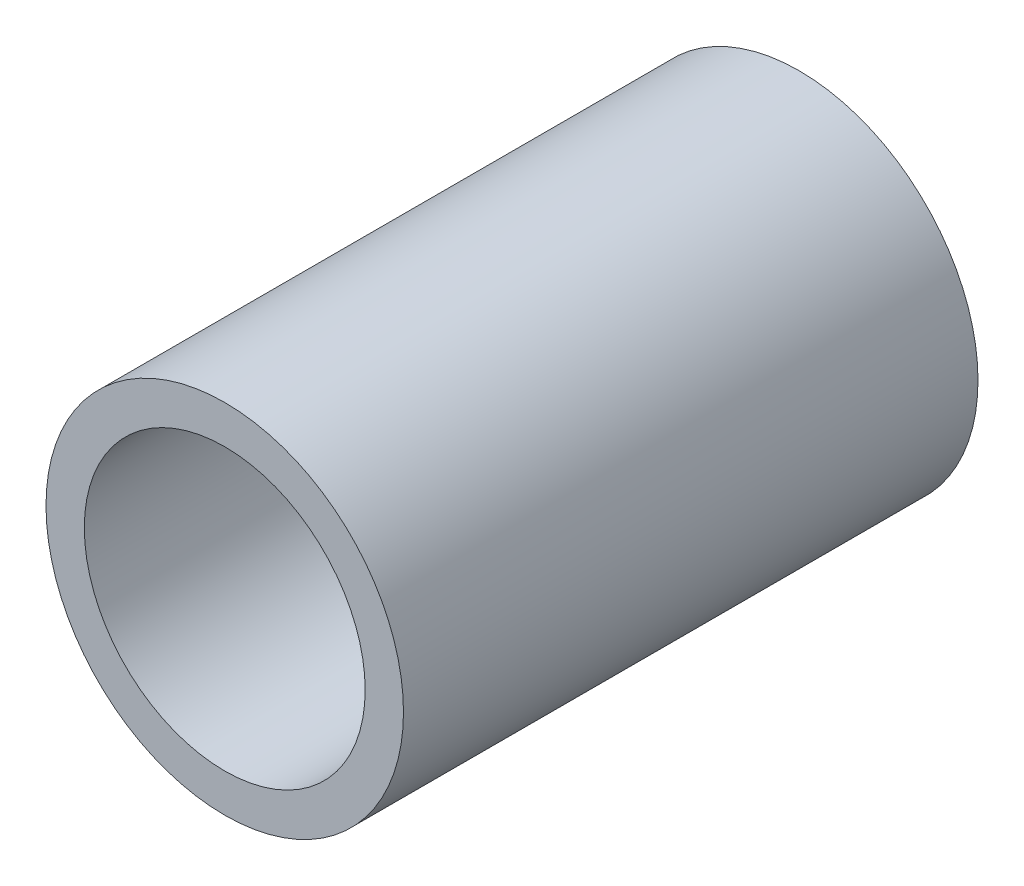
SolidWorks part; units mm, degrees
material "Сплав 2024"
ref_plane "Спереди" through (0, 0, 0) normal (0, 0, 1) x (1, 0, 0)
ref_plane "Сверху" through (0, 0, 0) normal (0, 1, 0) x (1, 0, 0)
ref_plane "Справа" through (0, 0, 0) normal (1, 0, 0) x (0, 0, -1)
sketch "Эскиз1" plane through (0, 0, 0) normal (0, 0, 1) x (1, 0, 0)
  circle A0 centre (0, 0) radius 14
  dimension "D1" = 28
extrude "Бобышка-Вытянуть1" add sketch "Эскиз1" along normal blind 45
ref_plane "Плоскость1" through (0, 14, 0) normal (0, 1, 0) x (1, 0, 0)
sketch "Эскиз2" plane through (0, 14, 0) normal (0, 1, 0) x (1, 0, 0)
  line L0 (0, 0) -> (0, -45) construction
  line L1 (-14, -45) -> (14, -45) construction
  line L2 (14, 0) -> (-14, 0) construction
  line L11 (-1.5, -24.8972) -> (1.5, -45) construction
  line L12 (-1.5, -45) -> (1.5, -24.8972) construction
  arc A0 (1.5, -24.8972) -> (-1.5, -24.8972) centre (0, -14) ccw
  arc A1 (-1.5, -24.8972) -> (1.5, -24.8972) centre (0, -14) ccw
  point P9 (0, -12.5)
  point P10 (0, -34.9486)
  point P17 (12.5, -12.5)
  dimension "D1" = 22
  dimension "D2" = 14
extrude "Вырез-Вытянуть1" [suppressed] cut sketch "Эскиз2" against normal through all
sketch "Эскиз3" [suppressed] plane through (0, 14, 0) normal (0, 1, 0) x (1, 0, 0)
  line L0 (14, -45) -> (14, 0) construction
  line L1 (14, 0) -> (-14, 0) construction
  line L2 (0, 0) -> (14, 0)
  line L3 (14, 0) -> (14, -14)
  arc A0 (14, -14) -> (0, 0) centre (0, -14) ccw
extrude "Вырез-Вытянуть2" [suppressed] cut sketch "Эскиз3" against normal through all
mirror "Зеркальное отражение1" [suppressed] about plane through (0, 0, 0) normal (1, 0, 0)
sketch "Эскиз5" plane through (0, 0, 45) normal (0, 0, 1) x (1, 0, 0)
  circle A0 centre (0, 0) radius 11
  dimension "D1" = 22
extrude "Вырез-Вытянуть3" cut sketch "Эскиз5" against normal blind 31
ref_plane "Плоскость2" through (-14, 0, 0) normal (-1, 0, 0) x (0, 0, 1)
sketch "Эскиз7" [suppressed] plane through (-14, 0, 0) normal (-1, 0, 0) x (0, 0, 1)
  line L0 (45, 0) -> (0, 0) construction
  line L1 (45, -14) -> (45, 14) construction
  line L2 (35, 13.9194) -> (35, -13.9194) construction
  line L3 (45, 13.9194) -> (24.8972, 13.9194) construction
  line L4 (24.8972, -13.9194) -> (45, -13.9194) construction
  dimension "D1" = 10
hole_wizard "Отверстие с зазором M41" [suppressed] positions "Эскиз9" profile "Эскиз8" hole size "M4" standard "Ansi Metric"
sketch "Эскиз9" [suppressed] plane through (-14, 0, 0) normal (-1, 0, 0) x (0, 0, 1)
  line L0 (45, 0) -> (0, 0) construction
  line L1 (35, 13.9194) -> (35, -13.9194) construction
  point P0 (35, 0)
sketch "Эскиз8" plane through (-14, 0, 35) normal (0, 1, 0) x (0, 0, 1)
  line L0 (0, 0) -> (0, 6.3519)
  line L1 (0, 6.3519) -> (2.25, 5)
  line L2 (2.25, 5) -> (2.25, 0)
  line L5 (2.25, 0) -> (0, 0)
  line L10 (0, 6.3519) -> (-2.25, 5) construction
  line L11 (0, -6.35) -> (0, 107.95) construction
  dimension "Диаметр отверстия" = 4.5
  dimension "Глубина отверстия" = 5
  dimension "Угол заточки сверла" = 118
sketch "Эскиз10" [suppressed] plane through (0, 14, 0) normal (0, 1, 0) x (1, 0, 0)
  line L0 (0, 0) -> (0, -50) construction
  circle A0 centre (0, -22) radius 4
  arc A1 (14, -14) -> (-14, -14) centre (0, -14) ccw construction
  arc A2 (1.5, -24.8972) -> (-1.5, -24.8972) centre (0, -14) ccw construction
  dimension "D1" = 8
  dimension "D2" = 8
extrude "Вырез-Вытянуть5" [suppressed] cut sketch "Эскиз10" against normal through all
fillet "Скругление2" [suppressed] radius 3
ref_plane "Плоскость3" through (14, 0, 0) normal (1, 0, 0) x (0, 0, -1)
hole_wizard "Отверстие обработанное метчиком M4x0.71" [suppressed] positions "Эскиз12" profile "Эскиз11" tap size "M4x0.7" standard "Ansi Metric"
sketch "Эскиз12" [suppressed] plane through (14, 0, 0) normal (1, 0, 0) x (0, 0, -1)
  line L0 (-45, 0) -> (0, 0) construction
  line L1 (-35, 13.9194) -> (-35, -13.9194) construction
  point P0 (-35, 0)
sketch "Эскиз11" plane through (14, 0, 35) normal (0, 1, 0) x (0, 0, -1)
  line L0 (0, 0) -> (0, 12.4914)
  line L1 (0, 12.4914) -> (1.65, 11.5)
  line L2 (1.65, 11.5) -> (1.65, 0)
  line L5 (1.65, 0) -> (0, 0)
  line L10 (0, 12.4914) -> (-1.65, 11.5) construction
  line L11 (0, -6.35) -> (0, 107.95) construction
  dimension "Диаметр сверла" = 3.3
  dimension "Глубина сверла" = 11.5
  dimension "Угол заточки сверла" = 118
cosmetic thread "Отверстие резьбы1" [suppressed] parameters "D1"=3.1245, "D2"=4
